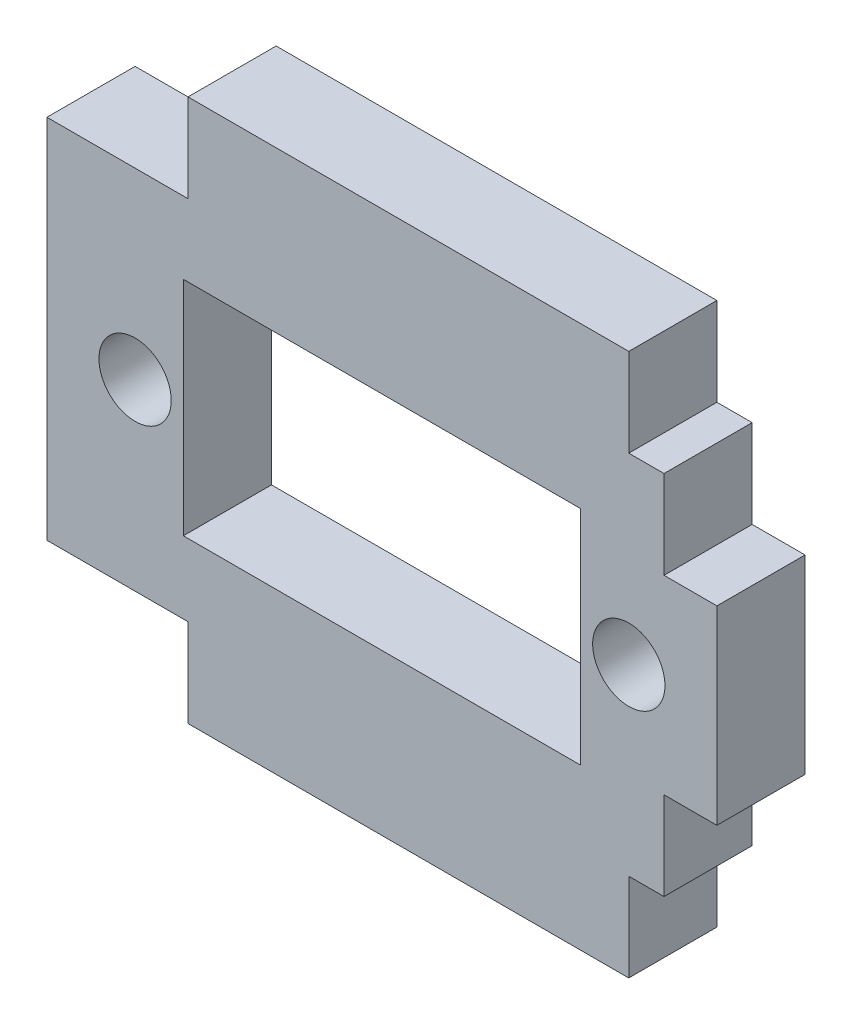
SolidWorks part; units mm, degrees
material "Acrílico (Impacto medio-alto)"
ref_plane "Alzado" through (0, 0, 0) normal (0, 0, 1) x (1, 0, 0)
ref_plane "Planta" through (0, 0, 0) normal (0, 1, 0) x (1, 0, 0)
ref_plane "Vista lateral" through (0, 0, 0) normal (1, 0, 0) x (0, 0, -1)
sketch "Croquis1" plane through (0, 0, 0) normal (0, 0, 1) x (1, 0, 0)
  line L5 (-12.5, 15.39) -> (12.5, 15.39)
  line L15 (-12.5, -15.39) -> (12.5, -15.39) construction
  line L16 (-12.5, -15.39) -> (-12.5, 15.39) construction
  line L18 (-12.5, 15.39) -> (12.5, 15.39) construction
  line L25 (12.5, -15.39) -> (12.5, 15.39) construction
  line L26 (-12.5, -15.39) -> (12.5, 15.39) construction
  line L27 (-12.5, 15.39) -> (12.5, -15.39) construction
  line L28 (12.5, 15.39) -> (12.5, 10.39)
  line L29 (12.5, 10.39) -> (14.5, 10.39)
  line L30 (14.5, 10.39) -> (14.5, 5.39)
  line L31 (14.5, 5.39) -> (17.5, 5.39)
  line L32 (17.5, 5.39) -> (17.5, -5.39)
  line L33 (17.5, 0) -> (0, 0) construction
  line L34 (0, 0) -> (-20.5, 0) construction
  line L35 (-12.5, 15.39) -> (-12.5, 10.39)
  line L36 (-12.5, 10.39) -> (-20.5, 10.39)
  line L37 (-20.5, 10.39) -> (-20.5, -10.39)
  line L38 (12.5, -10.39) -> (14.5, -10.39)
  line L39 (14.5, -5.39) -> (17.5, -5.39)
  line L40 (14.5, -10.39) -> (14.5, -5.39)
  line L41 (12.5, -15.39) -> (12.5, -10.39)
  line L42 (-12.5, -15.39) -> (12.5, -15.39)
  line L43 (-12.5, -15.39) -> (-12.5, -10.39)
  line L44 (-12.5, -10.39) -> (-20.5, -10.39)
  point P26 (0, 0)
  dimension "D3" = 8
  dimension "D6" = 25
  dimension "D7" = 2
  dimension "D8" = 5
  dimension "D9" = 10.78
  dimension "D10" = 5
  dimension "D11" = 5
extrude "Saliente-Extruir1" add sketch "Croquis1" along normal blind 5 contours L44 L43 L42 L41 L38 L40 L39 L32 L31 L30 L29 L28 L5 L35 L36 L37
sketch "Croquis2" plane through (0, 0, 5) normal (0, 0, 1) x (1, 0, 0)
  line L0 (-15.5, 0) -> (3.4674, 0) construction
  line L1 (3.4674, 0) -> (12.5035, 0) construction
  line L2 (-20.5, 10.39) -> (-20.5, -10.39) construction
  line L5 (-12.7634, -6.3) -> (9.7666, -6.3)
  line L6 (-12.7634, -6.3) -> (-12.7634, 6.3)
  line L7 (-12.7634, 6.3) -> (9.7666, 6.3)
  line L8 (9.7666, -6.3) -> (9.7666, 6.3)
  line L9 (-12.7634, -6.3) -> (9.7666, 6.3) construction
  line L10 (-12.7634, 6.3) -> (9.7666, -6.3) construction
  circle A0 centre (-15.5, 0) radius 2.05
  circle A1 centre (3.4674, 0) radius 3 construction
  circle A2 centre (12.5035, 0) radius 2.05
  point P1 (3.4674, 0)
  point P3 (-12.7634, -6.3)
  point P6 (13.2616, -20.3515)
  point P11 (-12.763, 0)
  point P14 (-20.5, 0)
  point P21 (-1.4984, 0)
  dimension "D3" = 6
  dimension "D4" = 4.1
  dimension "D6" = 22.53
  dimension "D1" = 16.2304
  dimension "D2" = 2.737
  dimension "D5" = 9.036
  dimension "D7" = 12.6
  dimension "D8" = 2.7369
  dimension "D9" = 5
extrude "Cut-Extrude1" cut sketch "Croquis2" against normal up to next
